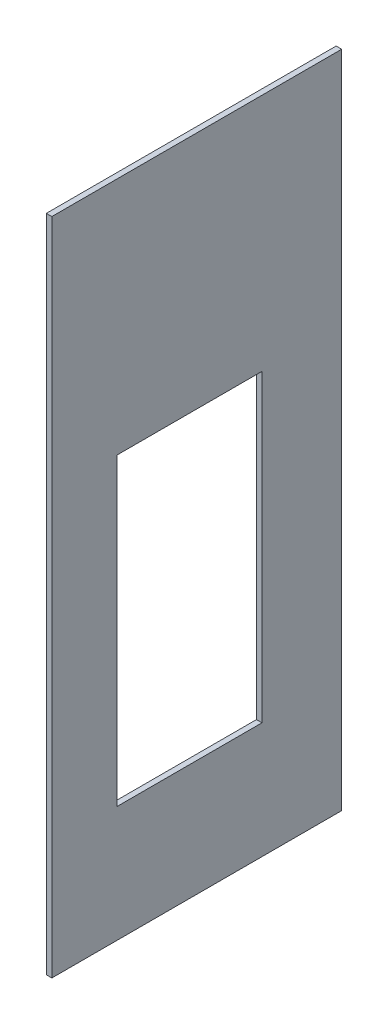
SolidWorks part; units mm, degrees
ref_plane "Front Plane" through (0, 0, 0) normal (0, 0, 1) x (1, 0, 0)
ref_plane "Top Plane" through (0, 0, 0) normal (0, 1, 0) x (1, 0, 0)
ref_plane "Right Plane" through (0, 0, 0) normal (1, 0, 0) x (0, 0, -1)
sketch "Sketch1" plane through (0, 0, 0) normal (1, 0, 0) x (0, 0, -1)
  line L1 (-31.75, -72.2313) -> (31.75, -72.2313)
  line L2 (-31.75, -72.2313) -> (-31.75, 72.2313)
  line L3 (-31.75, 72.2313) -> (31.75, 72.2313)
  line L4 (31.75, -72.2313) -> (31.75, 72.2313)
  line L5 (-31.75, -72.2313) -> (31.75, 72.2313) construction
  line L6 (-31.75, 72.2313) -> (31.75, -72.2313) construction
  point P0 (0, 0)
  dimension "D1" = 63.5
  dimension "D2" = 144.4625
extrude "Boss-Extrude1" add sketch "Sketch1" along normal blind 1.2141 contours L2 L3 L4 L1
sketch "Sketch3" plane through (1.2141, 0, 0) normal (1, 0, 0) x (0, 0, -1)
  line L0 (-31.75, -72.2313) -> (-31.75, 72.2313) construction
  line L1 (-17.4625, -46.8312) -> (14.2875, -46.8312)
  line L2 (-17.4625, -46.8312) -> (-17.4625, 19.8438)
  line L3 (-17.4625, 19.8438) -> (14.2875, 19.8438)
  line L4 (14.2875, -46.8312) -> (14.2875, 19.8438)
  line L5 (-17.4625, -46.8312) -> (14.2875, 19.8438) construction
  line L6 (-17.4625, 19.8438) -> (14.2875, -46.8312) construction
  line L7 (-31.75, -72.2313) -> (31.75, -72.2313) construction
  point P0 (-1.5875, -13.4937)
  dimension "D1" = 31.75
  dimension "D2" = 66.675
  dimension "D3" = 14.2875
  dimension "D4" = 25.4
extrude "Cut-Extrude1" cut sketch "Sketch3" against normal through all
